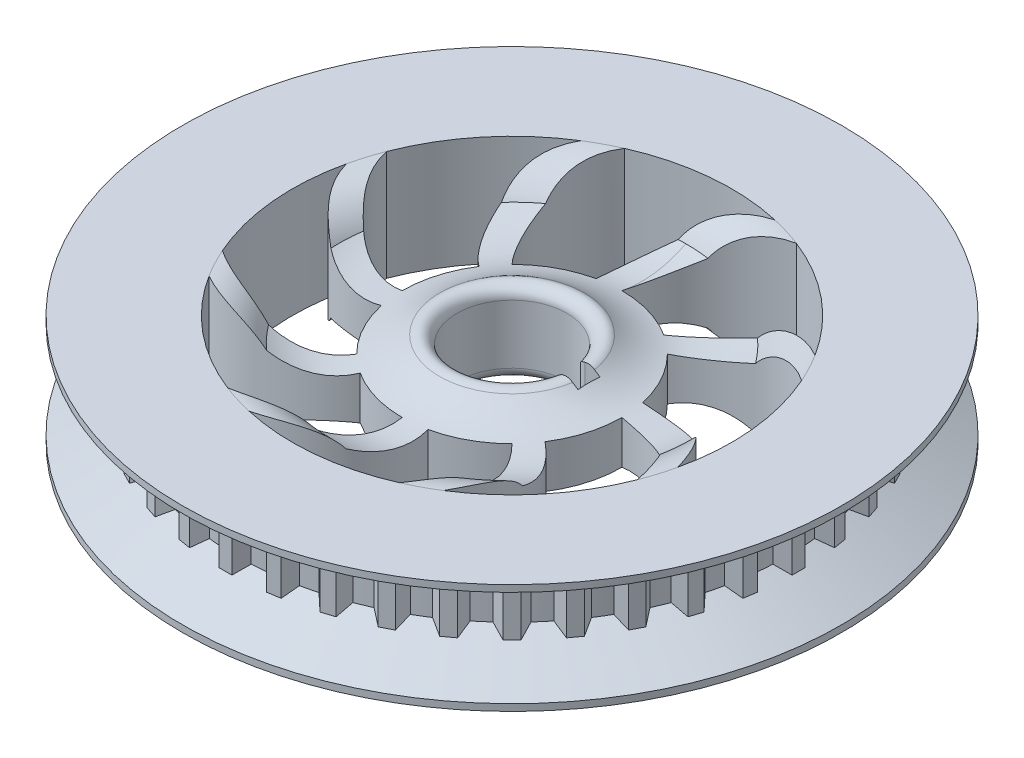
SolidWorks part; units mm, degrees
ref_plane "Front Plane" through (0, 0, 0) normal (0, 0, 1) x (1, 0, 0)
ref_plane "Top Plane" through (0, 0, 0) normal (0, 1, 0) x (1, 0, 0)
ref_plane "Right Plane" through (0, 0, 0) normal (1, 0, 0) x (0, 0, -1)
sketch "Sketch1" plane through (0, 0, 0) normal (0, 1, 0) x (1, 0, 0)
  line L1 (0, 1) -> (7, 1)
  line L2 (0, 1) -> (0, -1)
  line L3 (0, -1) -> (7, -1)
  line L4 (7, 1) -> (7, -1)
  circle A0 centre (0, 0) radius 5
  circle A1 centre (0, 0) radius 30
  dimension "D1" = 10
  dimension "D6" = 60
  dimension "D2" = 2
  dimension "D3" = 1
  dimension "D4" = 7
  dimension "D5" = 7
extrude "Boss-Extrude1" add sketch "Sketch1" along normal blind 10 contours A1 A0 L1 L4 L3
sketch "Sketch2" plane through (0, 0, 0) normal (0, 0, 1) x (1, 0, 0)
  line L0 (30, 10) -> (-30, 10) construction
  line L1 (4.899, 10) -> (-5, 10) construction
  line L2 (-22.4019, 5) -> (-5, 5)
  line L3 (-5, 0) -> (-5, 10)
  line L4 (-22.4019, 5) -> (-30, 9.3868)
  line L5 (-30, 0.6132) -> (-22.4019, 5)
  line L6 (-30, 9.3868) -> (-30, 0.6132)
  line L7 (0, 0) -> (0, 8.2709) construction
  line L8 (-30, 10) -> (-5, 10)
  line L9 (-30, 10) -> (-30, 0)
  line L10 (-30, 0) -> (-5, 0)
  line L11 (-5, 10) -> (-5, 0)
  line L12 (-25, 6.5) -> (-25, 3.5)
  line L13 (-25, 3.5) -> (-22.4019, 5)
  circle A0 centre (-20, 5) radius 5
  arc A1 (-15.8249, 7.7512) -> (-5, 10) centre (-11.8044, 15.5756) ccw
  arc A2 (-15.8249, 2.2488) -> (-5, 0) centre (-11.8044, -5.5756) cw
  arc A3 (-15.8249, 7.7512) -> (-5, 10) centre (-11.8044, 15.5756) ccw
  arc A4 (-15.8249, 2.2488) -> (-5, 0) centre (-11.8044, -5.5756) cw
  point P22 (-25, 5)
  dimension "D1" = 10
  dimension "D2" = 5
  dimension "D4" = 8.797
  dimension "D3" = 20
  dimension "D5" = 15
  dimension "D6" = 2.7512
  dimension "D7" = 7.5981
  dimension "D8" = 10
  dimension "D9" = 0.6132
  dimension "D11" = 0.6132
revolve "Cut-Revolve2" cut sketch "Sketch2" angle 360 about L7
sketch "Sketch4" plane through (0, 10, 0) normal (0, 1, 0) x (1, 0, 0)
  circle A0 centre (0, 0) radius 20
  circle A1 centre (0, 0) radius 10
  arc A2 (0, 10) -> (7.2361, 18.6451) centre (8.9982, 9.8193) cw
  arc A3 (-2.1248, 9.7717) -> (4.4229, 19.5048) centre (6.813, 10.828) cw
  arc A4 (5.4072, 8.4121) -> (16.9194, 10.6646) centre (12.4741, 2.839) cw
  arc A5 (7.0711, 7.0711) -> (18.3007, 8.0674) centre (13.306, 0.5806) cw
  arc A6 (9.7717, 2.1248) -> (19.5048, -4.4229) centre (10.828, -6.813) cw
  arc A7 (10, 0) -> (18.6451, -7.2361) centre (9.8193, -8.9982) cw
  arc A8 (8.4121, -5.4072) -> (10.6646, -16.9194) centre (2.839, -12.4741) cw
  arc A9 (7.0711, -7.0711) -> (8.0674, -18.3007) centre (0.5806, -13.306) cw
  arc A10 (2.1248, -9.7717) -> (-4.4229, -19.5048) centre (-6.813, -10.828) cw
  arc A11 (0, -10) -> (-7.2361, -18.6451) centre (-8.9982, -9.8193) cw
  arc A12 (-5.4072, -8.4121) -> (-16.9194, -10.6646) centre (-12.4741, -2.839) cw
  arc A13 (-7.0711, -7.0711) -> (-18.3007, -8.0674) centre (-13.306, -0.5806) cw
  arc A14 (-9.7717, -2.1248) -> (-19.5048, 4.4229) centre (-10.828, 6.813) cw
  arc A15 (-10, 0) -> (-18.6451, 7.2361) centre (-9.8193, 8.9982) cw
  arc A16 (-8.4121, 5.4072) -> (-10.6646, 16.9194) centre (-2.839, 12.4741) cw
  arc A17 (-7.0711, 7.0711) -> (-8.0674, 18.3007) centre (-0.5806, 13.306) cw
  point P55 (0, 0)
  circle M1 centre (0, 0) radius 20
  dimension "D1" = 40
  dimension "D2" = 20
  dimension "D4" = 9
  dimension "D5" = 9
  dimension "D9" = 5.4072
  dimension "D3" = 19.5048
  dimension "D6" = 2.1248
  dimension "D7" = 2.8132
  dimension "D10" = 10
  dimension "D8" = 8
extrude "Cut-Extrude1" cut sketch "Sketch4" against normal through all contours A17 A1 A3 M1 | A1 A4 A2 M1 | A1 A6 A5 M1 | A1 A8 A7 M1 | A1 A10 A9 M1 | A1 A12 A11 M1 | A1 A14 A13 M1 | A1 A16 A15 M1
fillet "Fillet1" radius 1 4 edges at (4.899, 5, 1) (-5, 10, 0) (4.899, 5, -1) (-5, 0, 0)
ref_plane "Plane1" through (0, 6, 0) normal (0, -1, 0) x (-1, 0, 0)
sketch "Sketch5" plane through (0, 6, 0) normal (0, -1, 0) x (-1, 0, 0)
  line L0 (0.5822, 26.0834) -> (-0.5822, 26.0834)
  line L1 (0, 27.0918) -> (-1.8115, 23.9541)
  line L2 (-1.8115, 23.9541) -> (1.8115, 23.9541)
  line L3 (1.8115, 23.9541) -> (0, 27.0918)
  circle A0 centre (0, 25) radius 1.0459 construction
  circle A1 centre (0, 0) radius 25 construction
  dimension "D1" = 23.9541
  dimension "D2" = 3.1377
  dimension "D3" = 1.8115
  dimension "D4" = 1.2294
extrude "Boss-Extrude2" add sketch "Sketch5" along normal blind 4 and the other way blind 2 contours L2 L3 L0 L1
pattern_circular "CirPattern1" count 40 over 360 about axis through (0, 0, 0) along (0, 1, 0) of "Boss-Extrude2"
